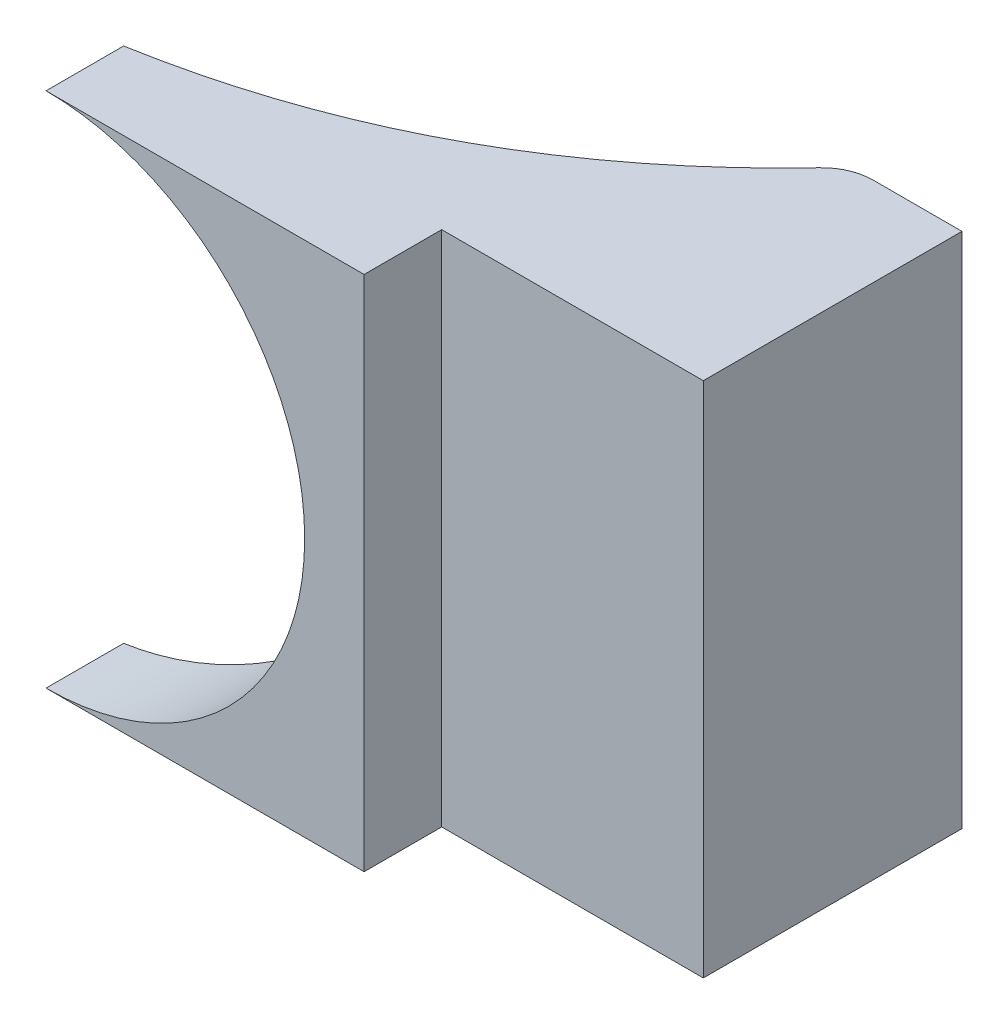
SolidWorks part; units mm, degrees
ref_plane "Front Plane" through (0, 0, 0) normal (0, 0, 1) x (1, 0, 0)
ref_plane "Top Plane" through (0, 0, 0) normal (0, 1, 0) x (1, 0, 0)
ref_plane "Right Plane" through (0, 0, 0) normal (1, 0, 0) x (0, 0, -1)
sketch "Sketch1" plane through (0, 0, 0) normal (0, 0, 1) x (1, 0, 0)
  line L0 (0, -1067.9916) -> (0, 52331.5874) construction
  line L1 (-1067.9916, 0) -> (52331.5874, 0) construction
  line L6 (0, 50) -> (112.0608, 50)
  line L7 (112.0608, 50) -> (112.0608, -50)
  line L8 (112.0608, -50) -> (0, -50)
  circle A1 centre (0, 0) radius 50
  dimension "D1" = 100
  dimension "D2" = 100
extrude "Boss-Extrude1" add sketch "Sketch1" along normal blind 50 contours A1 L8 L7 L6
sketch "Sketch2" plane through (0, 0, 0) normal (0, 1, 0) x (1, 0, 0)
  line L3 (0, 0) -> (112.0608, 0) construction
  line L4 (90.4904, 0) -> (0, 0)
  line L5 (0, 0) -> (0, -50)
  spline S0 degree 2 poles (0, -50) (54.3212, -40.5055) (90.4904, 0) knots 0 0 0 1 1 1
extrude "Cut-Extrude1" cut sketch "Sketch2" against normal blind 98 and the other way blind 122
fillet "Fillet1" radius 10 1 edges at (90.4904, 0, 0)
sketch "Sketch3" plane through (0, 0, 50) normal (0, 0, 1) x (1, 0, 0)
  line L0 (0, 50) -> (61.4868, 50)
  line L1 (0, 50) -> (112.0608, 50) construction
  line L2 (61.4868, 50) -> (61.4868, -50)
  line L3 (112.0608, -50) -> (0, -50) construction
  line L4 (61.4868, -50) -> (0, -50)
  arc A0 (0, -50) -> (0, 50) centre (0, 0) ccw
extrude "Boss-Extrude2" add sketch "Sketch3" along normal blind 15
